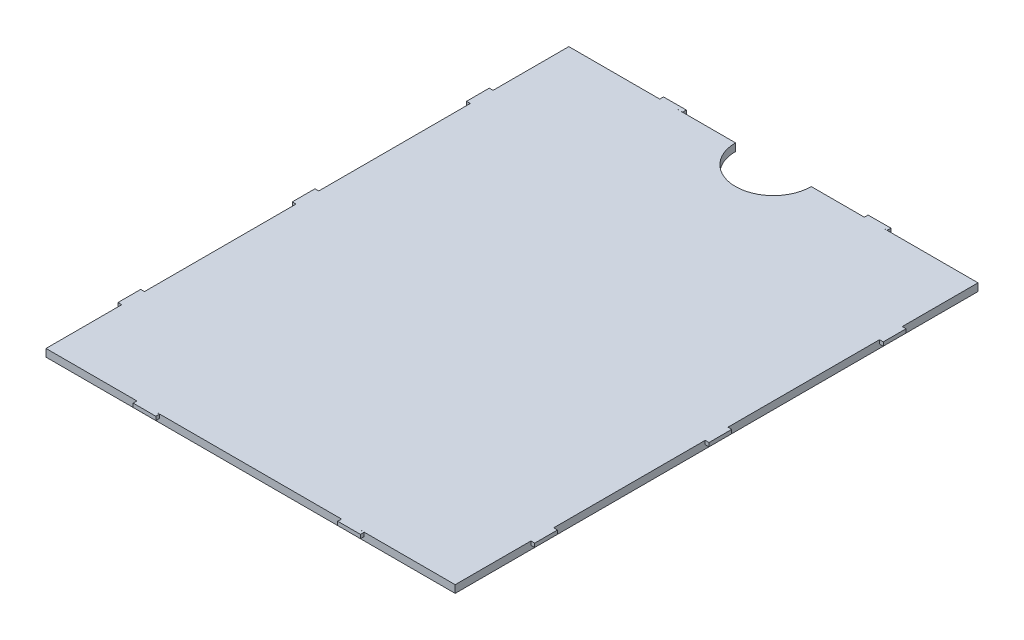
SolidWorks part; units mm, degrees
ref_plane "Front Plane" through (0, 0, 0) normal (0, 0, 1) x (1, 0, 0)
ref_plane "Top Plane" through (0, 0, 0) normal (0, 1, 0) x (1, 0, 0)
ref_plane "Right Plane" through (0, 0, 0) normal (1, 0, 0) x (0, 0, -1)
sketch "Sketch1" plane through (0, 34.2741, 0) normal (0, -1, 0) x (1, 0, 0)
  line L0 (-13.1013, 96.8075) -> (-60.1013, 96.8075) construction
  line L1 (-67.1013, 96.8075) -> (-13.1013, 96.8075)
  line L2 (-67.1013, 96.8075) -> (-67.1013, 27.8075)
  line L3 (-67.1013, 27.8075) -> (-13.1013, 27.8075)
  line L4 (-13.1013, 96.8075) -> (-13.1013, 27.8075)
extrude "Boss-Extrude1" add sketch "Sketch1" against normal blind 1
sketch "Sketch3" plane through (0, 34.2741, 0) normal (0, -1, 0) x (1, 0, 0)
  line L0 (-13.1013, 37.8075) -> (-13.1013, 40.8075)
  line L1 (-13.1013, 37.8075) -> (-12.6013, 37.8075)
  line L2 (-13.1013, 40.8075) -> (-12.6013, 40.8075)
  line L3 (-12.6013, 37.8075) -> (-12.6013, 40.8075)
  line L4 (-13.1013, 37.8075) -> (-12.6013, 40.8075) construction
  line L5 (-13.1013, 40.8075) -> (-12.6013, 37.8075) construction
  line L6 (-67.1013, 27.8075) -> (-40.1013, 27.8075)
  line L7 (-67.1013, 96.8075) -> (-13.1013, 96.8075)
  line L8 (-67.1013, 96.8075) -> (-67.1013, 27.8075)
  line L9 (-67.1013, 27.8075) -> (-13.1013, 27.8075)
  line L10 (-13.1013, 96.8075) -> (-13.1013, 27.8075)
  line L11 (-67.1013, 96.8075) -> (-13.1013, 96.8075)
  line L12 (-67.1013, 96.8075) -> (-67.1013, 27.8075)
  line L13 (-67.1013, 27.8075) -> (-13.1013, 27.8075)
  line L14 (-13.1013, 96.8075) -> (-13.1013, 27.8075)
  line L15 (-40.1013, 27.8075) -> (-13.1013, 27.8075)
  line L16 (-13.1013, 27.8075) -> (-13.1013, 50.8075)
  line L17 (-13.1013, 50.8075) -> (-13.1013, 73.8075)
  line L18 (-13.1013, 73.8075) -> (-13.1013, 96.8075)
  line L19 (-13.1013, 73.8075) -> (-13.1013, 27.8075)
  line L20 (-13.1013, 27.8075) -> (-13.1013, 50.8075) construction
  line L21 (-28.1013, 27.811) -> (-25.1013, 27.804)
  line L22 (-28.1013, 27.811) -> (-28.1024, 27.311)
  line L23 (-25.1013, 27.804) -> (-25.1024, 27.304)
  line L24 (-28.1024, 27.311) -> (-25.1024, 27.304)
  line L25 (-28.1013, 27.811) -> (-25.1024, 27.304) construction
  line L26 (-25.1013, 27.804) -> (-28.1024, 27.311) construction
  line L27 (-55.1013, 27.811) -> (-52.1013, 27.804)
  line L28 (-52.1013, 27.804) -> (-52.1024, 27.304)
  line L29 (-55.1024, 27.311) -> (-52.1024, 27.304)
  line L30 (-55.1013, 27.811) -> (-55.1024, 27.311)
  line L31 (-52.1013, 27.804) -> (-55.1024, 27.311) construction
  line L32 (-55.1013, 27.811) -> (-52.1024, 27.304) construction
  line L33 (-13.1013, 62.3075) -> (-67.1013, 62.3075) construction
  line L34 (-55.1013, 96.804) -> (-55.1024, 97.304)
  line L35 (-55.1024, 97.304) -> (-52.1024, 97.311)
  line L36 (-52.1013, 96.811) -> (-52.1024, 97.311)
  line L37 (-55.1013, 96.804) -> (-52.1013, 96.811)
  line L38 (-28.1013, 96.804) -> (-28.1024, 97.304)
  line L39 (-28.1024, 97.304) -> (-25.1024, 97.311)
  line L40 (-25.1013, 96.811) -> (-25.1024, 97.311)
  line L41 (-28.1013, 96.804) -> (-25.1013, 96.811)
  line L42 (-13.1013, 27.8075) -> (-13.1013, 39.3075)
  line L43 (-13.1013, 60.8075) -> (-13.1013, 63.8075)
  line L44 (-13.1013, 63.8075) -> (-12.6013, 63.8075)
  line L45 (-12.6013, 60.8075) -> (-12.6013, 63.8075)
  line L46 (-13.1013, 60.8075) -> (-12.6013, 60.8075)
  line L47 (-13.1013, 83.8075) -> (-13.1013, 86.8075)
  line L48 (-13.1013, 86.8075) -> (-12.6013, 86.8075)
  line L49 (-12.6013, 83.8075) -> (-12.6013, 86.8075)
  line L50 (-13.1013, 83.8075) -> (-12.6013, 83.8075)
  line L51 (-40.1013, 27.8075) -> (-40.1013, 96.8075) construction
  line L52 (-67.1013, 83.8075) -> (-67.6013, 83.8075)
  line L53 (-67.6013, 83.8075) -> (-67.6013, 86.8075)
  line L54 (-67.1013, 86.8075) -> (-67.6013, 86.8075)
  line L55 (-67.1013, 83.8075) -> (-67.1013, 86.8075)
  line L56 (-67.1013, 60.8075) -> (-67.6013, 60.8075)
  line L57 (-67.6013, 60.8075) -> (-67.6013, 63.8075)
  line L58 (-67.1013, 63.8075) -> (-67.6013, 63.8075)
  line L59 (-67.1013, 60.8075) -> (-67.1013, 63.8075)
  line L60 (-67.1013, 37.8075) -> (-67.6013, 37.8075)
  line L61 (-67.6013, 37.8075) -> (-67.6013, 40.8075)
  line L62 (-67.1013, 40.8075) -> (-67.6013, 40.8075)
  line L63 (-67.1013, 37.8075) -> (-67.1013, 40.8075)
  point P0 (-26.6018, 27.5575)
  point P2 (-12.8513, 39.3075)
  point P7 (-40.1013, 27.8075)
  point P14 (-53.6013, 27.8075)
  point P16 (-26.6013, 27.8075)
  point P21 (-13.1013, 50.8075)
  point P24 (-26.6013, 27.8075)
  point P38 (-13.1013, 39.3075)
  point P41 (-13.1013, 39.3075)
  line M4 (-13.1013, 27.8075) -> (-13.1013, 96.8075)
  dimension "D1" = 3
  dimension "D2" = 0.5
  dimension "D3" = 3
  dimension "D4" = 23
  dimension "D5" = 23
  dimension "D6" = 0.5
  dimension "D7" = 2
  dimension "D8" = 11.5
  dimension "D9" = 3
extrude "Boss-Extrude2" add sketch "Sketch3" against normal blind 0.5 from offset 0.5 contours L12 L54 L53 L52 | L18 L50 L49 L48 | L19 L46 L45 L44 | L1 L3 L2 L19 M4 | L22 L24 L23 L21 L15 | L13 L30 L29 L28 L27 | L61 L62 L63 L60 | L57 L58 L59 L56 | L35 L36 L37 L34 | L39 L40 L41 L38 offset against normal yes
sketch "Sketch4" plane through (0, 34.2741, 0) normal (0, -1, 0) x (1, 0, 0)
  line L0 (-67.1013, 27.8075) -> (-13.1013, 27.8075) construction
  circle A0 centre (-40.1013, 27.8075) radius 5
  dimension "D1" = 10
extrude "Cut-Extrude1" cut sketch "Sketch4" against normal blind 1
